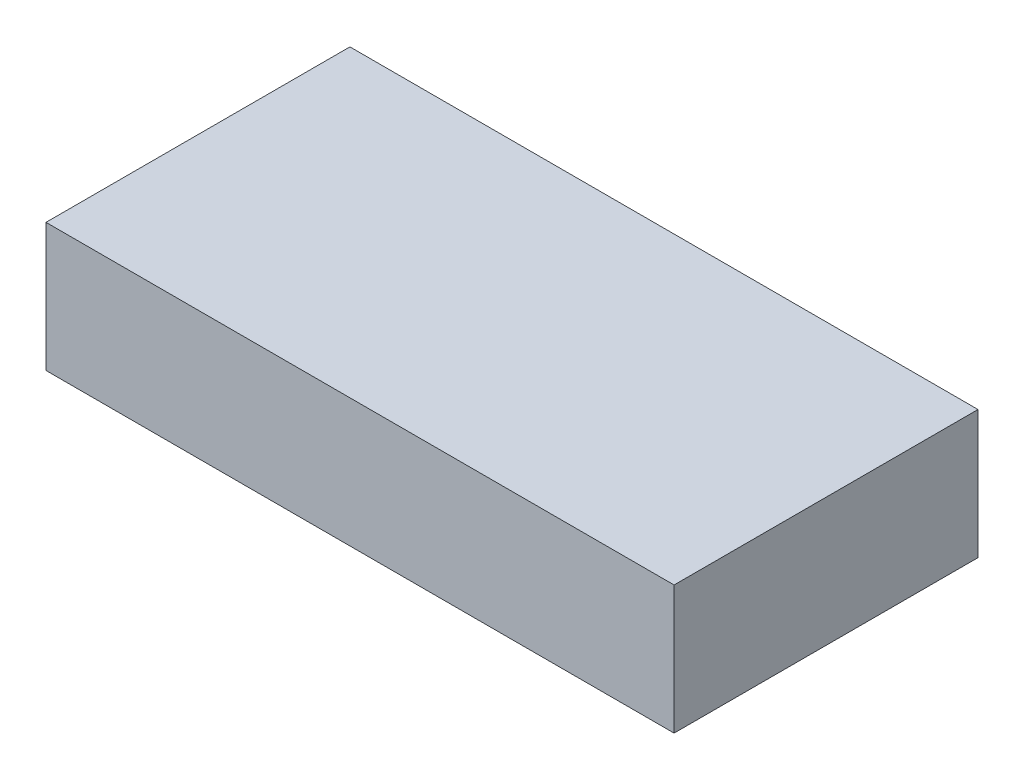
SolidWorks part; units mm, degrees
ref_plane "Front Plane" through (0, 0, 0) normal (0, 0, 1) x (1, 0, 0)
ref_plane "Top Plane" through (0, 0, 0) normal (0, 1, 0) x (1, 0, 0)
ref_plane "Right Plane" through (0, 0, 0) normal (1, 0, 0) x (0, 0, -1)
sketch "Sketch1" plane through (0, 0, 0) normal (0, 1, 0) x (1, 0, 0)
  line L1 (-23.1049, 12.7057) -> (47.7611, 12.7057)
  line L2 (-23.1049, 12.7057) -> (-23.1049, -21.5843)
  line L3 (-23.1049, -21.5843) -> (47.7611, -21.5843)
  line L4 (47.7611, 12.7057) -> (47.7611, -21.5843)
  dimension "D1" = 34.29
  dimension "D2" = 70.866
extrude "Boss-Extrude1" add sketch "Sketch1" along normal blind 14.478
equation "\"Battery Length\"= 2.7895in"
equation "\"battery width\"= 1.3515in"
equation "\"battery height\"= 0.5705in"
